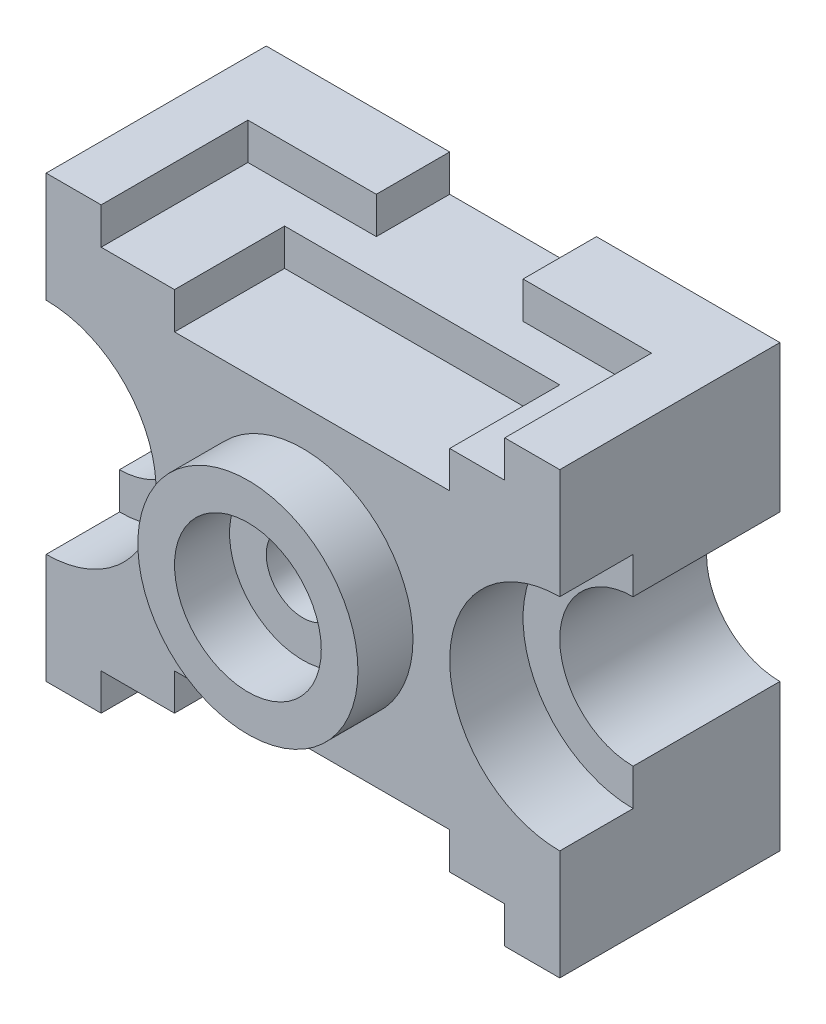
SolidWorks part; units mm, degrees
ref_plane "Front Plane" through (0, 0, 0) normal (0, 0, 1) x (1, 0, 0)
ref_plane "Top Plane" through (0, 0, 0) normal (0, 1, 0) x (1, 0, 0)
ref_plane "Right Plane" through (0, 0, 0) normal (1, 0, 0) x (0, 0, -1)
sketch "Sketch1" plane through (0, 0, 0) normal (0, 0, 1) x (1, 0, 0)
  line L0 (-15, -5) -> (-7.5, -5)
  line L1 (-7.5, -5) -> (-7.5, 0)
  line L2 (-7.5, 0) -> (0, 0)
  line L3 (0, 0) -> (0, 50)
  line L4 (0, 50) -> (-7.5, 50)
  line L5 (-7.5, 50) -> (-7.5, 55)
  line L6 (-7.5, 55) -> (-15, 55)
  line L7 (-15, 55) -> (-15, -5)
  dimension "D1" = 7.5
  dimension "D2" = 5
  dimension "D3" = 7.5
  dimension "D4" = 7.5
  dimension "D5" = 5
  dimension "D6" = 50
extrude "Boss-Extrude1" add sketch "Sketch1" along normal blind 30
sketch "Sketch3" plane through (0, 0, 0) normal (0, 0, -1) x (-1, 0, 0)
  line L0 (15, 55) -> (15, -5) construction
  line L1 (15, 35) -> (15, 15)
  arc A0 (15, 35) -> (15, 15) centre (15, 25) ccw
  dimension "D1" = 20
  dimension "D2" = 10
  dimension "D3" = 20
extrude "Cut-Extrude7" cut sketch "Sketch3" against normal blind 20
sketch "Sketch5" plane through (0, 50, 0) normal (0, 1, 0) x (1, 0, 0)
  line L0 (-7.5, 0) -> (10, 0)
  line L1 (10, 0) -> (10, -10)
  line L2 (10, -10) -> (-7.5, -10)
  line L3 (-7.5, -30) -> (-7.5, 0) construction
  line L4 (-7.5, -10) -> (-7.5, 0)
  dimension "D1" = 17.5
  dimension "10" = 10
extrude "Boss-Extrude2" add sketch "Sketch5" along normal blind 5
sketch "Sketch6" plane through (0, 0, 0) normal (0, 0, -1) x (-1, 0, 0)
  line L1 (0, 50) -> (-40, 50)
  line L2 (0, 50) -> (0, 0)
  line L3 (0, 0) -> (-40, 0)
  line L4 (-40, 50) -> (-40, 0)
  dimension "D1" = 40
extrude "Boss-Extrude3" add sketch "Sketch6" against normal blind 30
sketch "Sketch7" plane through (0, 0, 30) normal (0, 0, 1) x (1, 0, 0)
  line L0 (2.5, 50) -> (2.5, 45)
  line L1 (40, 50) -> (-7.5, 50) construction
  line L2 (2.5, 45) -> (40, 45)
  line L3 (40, 50) -> (40, 0) construction
  line L4 (40, 45) -> (40, 50)
  line L5 (40, 50) -> (2.5, 50)
  dimension "D1" = 5
  dimension "D2" = 37.5
extrude "Cut-Extrude11" cut sketch "Sketch7" against normal blind 15
sketch "Sketch8" plane through (0, 0, 30) normal (0, 0, 1) x (1, 0, 0)
  line L0 (2.5, 0) -> (2.5, 5)
  line L1 (-7.5, 0) -> (40, 0) construction
  line L2 (2.5, 5) -> (40, 5)
  line L3 (40, 45) -> (40, 0) construction
  line L4 (40, 5) -> (40, 0)
  line L5 (40, 0) -> (2.5, 0)
  dimension "D1" = 37.5
  dimension "D2" = 5
extrude "Cut-Extrude12" cut sketch "Sketch8" against normal blind 15
sketch "Sketch9" plane through (0, 0, 30) normal (0, 0, 1) x (1, 0, 0)
  line L0 (-15, 55) -> (-15, -5) construction
  line L1 (-15, 10) -> (-15, 40)
  arc A0 (-15, 40) -> (-15, 10) centre (-15, 25) cw
  dimension "D1" = 15
  dimension "D2" = 15
extrude "Cut-Extrude13" cut sketch "Sketch9" against normal blind 10
sketch "Sketch10" plane through (0, 0, 30) normal (0, 0, 1) x (1, 0, 0)
  line L0 (40, 45) -> (40, 5) construction
  circle A0 centre (20, 25) radius 15
  dimension "30" = 30
  dimension "D2" = 20
  dimension "D3" = 20
extrude "Boss-Extrude4" add sketch "Sketch10" along normal blind 7.5
sketch "Sketch11" plane through (0, 0, 37.5) normal (0, 0, 1) x (1, 0, 0)
  circle A0 centre (20, 25) radius 10
  dimension "10" = 20
extrude "Cut-Extrude14" cut sketch "Sketch11" against normal blind 7.5
sketch "Sketch12" plane through (0, 0, 30) normal (0, 0, 1) x (1, 0, 0)
  circle A0 centre (20, 25) radius 5
  dimension "D1" = 10
extrude "Cut-Extrude15" cut sketch "Sketch12" against normal blind 153.5
sketch "Sketch13" plane through (0, 0, 30) normal (0, 0, 1) x (1, 0, 0)
  line L0 (55, -5) -> (47.5, -5)
  line L1 (47.5, -5) -> (47.5, 0)
  line L2 (47.5, 0) -> (40, 0)
  line L3 (40, 0) -> (40, 50)
  line L4 (40, 50) -> (47.5, 50)
  line L5 (47.5, 50) -> (47.5, 55)
  line L6 (47.5, 55) -> (55, 55)
  line L7 (55, 55) -> (55, -5)
  dimension "D1" = 50
  dimension "D2" = 7.5
  dimension "D3" = 7.5
  dimension "D4" = 5
  dimension "D5" = 5
  dimension "D6" = 7.5
extrude "Boss-Extrude5" add sketch "Sketch13" against normal blind 30
sketch "Sketch14" plane through (0, 50, 0) normal (0, 1, 0) x (1, 0, 0)
  line L2 (47.5, 0) -> (30, 0)
  line L3 (10, 0) -> (47.5, 0) construction
  line L4 (30, 0) -> (30, -10)
  line L5 (30, -10) -> (47.5, -10)
  line L6 (47.5, 0) -> (47.5, -30) construction
  line L7 (47.5, -10) -> (47.5, 0)
  dimension "D1" = 10
  dimension "D2" = 17.5
extrude "Boss-Extrude6" add sketch "Sketch14" along normal blind 5
sketch "Sketch15" plane through (0, 0, 0) normal (0, 0, -1) x (-1, 0, 0)
  line L0 (-55, -5) -> (-55, 55) construction
  line L1 (-55, 35) -> (-55, 15)
  arc A0 (-55, 35) -> (-55, 15) centre (-55, 25) cw
  dimension "D1" = 20
  dimension "D2" = 20
extrude "Cut-Extrude16" cut sketch "Sketch15" against normal blind 20
sketch "Sketch16" plane through (0, 0, 30) normal (0, 0, 1) x (1, 0, 0)
  line L0 (55, -5) -> (55, 55) construction
  line L1 (55, 10) -> (55, 40)
  arc A0 (55, 40) -> (55, 10) centre (55, 25) ccw
  dimension "D1" = 15
  dimension "D3" = 15
  dimension "D2" = 15
extrude "Cut-Extrude17" cut sketch "Sketch16" against normal blind 10
